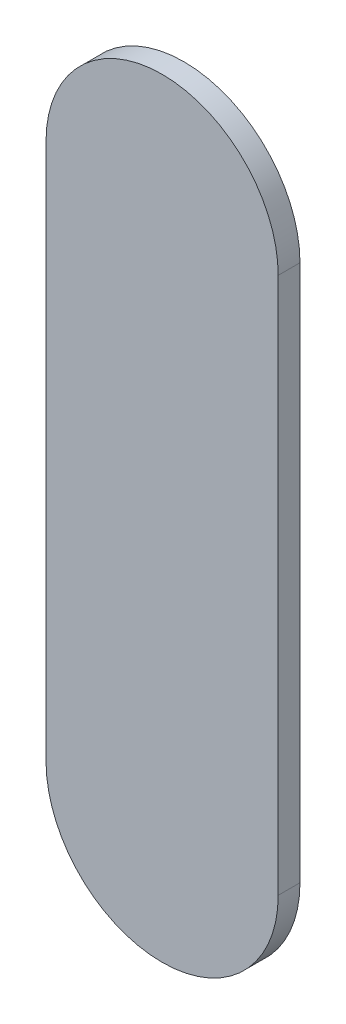
SolidWorks part; units mm, degrees
ref_plane "Спереди" through (0, 0, 0) normal (0, 0, 1) x (1, 0, 0)
ref_plane "Сверху" through (0, 0, 0) normal (0, 1, 0) x (1, 0, 0)
ref_plane "Справа" through (0, 0, 0) normal (1, 0, 0) x (0, 0, -1)
other "Configuration Table"
sketch "Sketch1" plane through (0, 0, 0) normal (0, 0, 1) x (1, 0, 0)
  line L0 (-8, 18.5) -> (-8, -18.5)
  line L1 (8, 18.5) -> (8, -18.5)
  arc A0 (8, 18.5) -> (-8, 18.5) centre (0, 18.5) ccw
  arc A1 (-8, -18.5) -> (8, -18.5) centre (0, -18.5) ccw
extrude "Boss-Extrude1" add sketch "Sketch1" along normal blind 1.5
